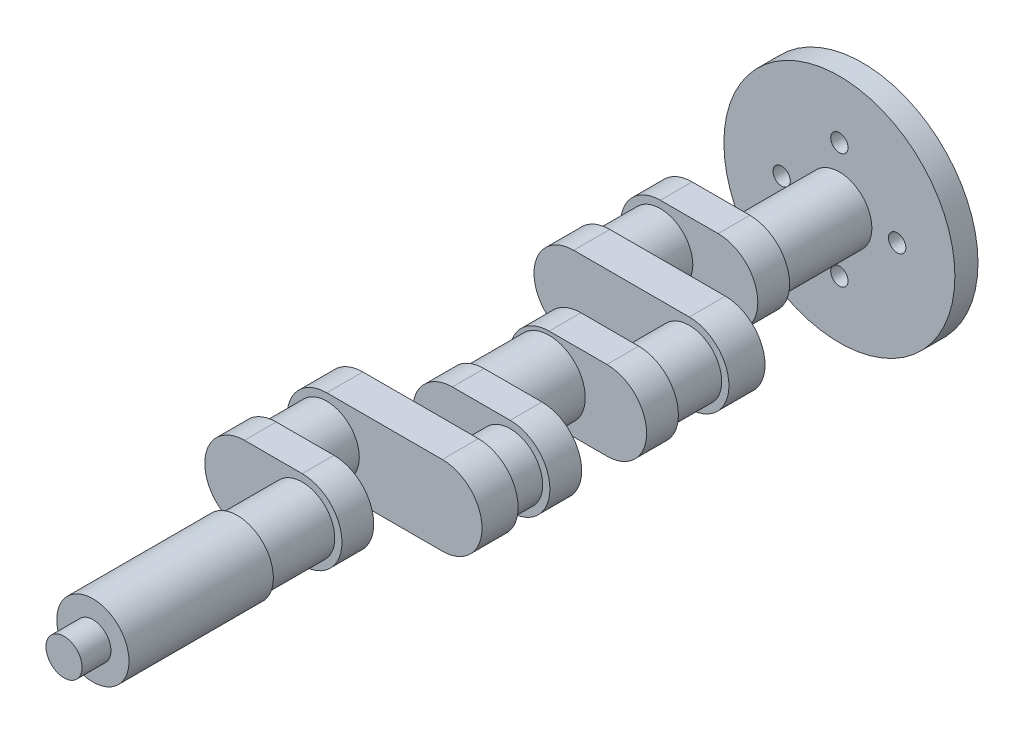
SolidWorks part; units mm, degrees
ref_plane "Front Plane" through (0, 0, 0) normal (0, 0, 1) x (1, 0, 0)
ref_plane "Top Plane" through (0, 0, 0) normal (0, 1, 0) x (1, 0, 0)
ref_plane "Right Plane" through (0, 0, 0) normal (1, 0, 0) x (0, 0, -1)
sketch "Sketch1" plane through (0, 0, 0) normal (0, 0, 1) x (1, 0, 0)
  circle A0 centre (0, 0) radius 80
  dimension "D1" = 160
extrude "Boss-Extrude1" add sketch "Sketch1" along normal blind 16
sketch "Sketch2" plane through (0, 0, 16) normal (0, 0, 1) x (1, 0, 0)
  circle A0 centre (0, 0) radius 22.5
  dimension "D1" = 45
extrude "Boss-Extrude2" add sketch "Sketch2" along normal blind 62
sketch "Sketch3" plane through (0, 0, 78) normal (0, 0, 1) x (1, 0, 0)
  line L0 (0, 0) -> (-40, 0) construction
  line L1 (0, -27.5) -> (-40, -27.5)
  line L2 (0, 27.5) -> (-40, 27.5)
  arc A0 (0, -27.5) -> (0, 27.5) centre (0, 0) ccw
  arc A1 (-40, 27.5) -> (-40, -27.5) centre (-40, 0) ccw
  point P3 (-20, 0)
  dimension "D1" = 27.5
  dimension "D2" = 40
extrude "Boss-Extrude3" add sketch "Sketch3" along normal blind 22
sketch "Sketch4" plane through (0, 0, 100) normal (0, 0, 1) x (1, 0, 0)
  circle A0 centre (-40, 0) radius 22.5
  dimension "D1" = 45
extrude "Boss-Extrude4" add sketch "Sketch4" along normal blind 35
sketch "Sketch5" plane through (0, 0, 135) normal (0, 0, 1) x (1, 0, 0)
  line L0 (-40, 0) -> (40, 0) construction
  line L1 (-40, 27.5) -> (40, 27.5)
  line L2 (-40, -27.5) -> (40, -27.5)
  arc A0 (-40, 27.5) -> (-40, -27.5) centre (-40, 0) ccw
  arc A1 (40, -27.5) -> (40, 27.5) centre (40, 0) ccw
  arc A3 (-40, 27.5) -> (-40, -27.5) centre (-40, 0) ccw construction
  point P4 (0, 0)
  point P9 (0, 0)
  dimension "D1" = 80
extrude "Boss-Extrude5" add sketch "Sketch5" along normal blind 25
sketch "Sketch6" plane through (0, 0, 160) normal (0, 0, 1) x (1, 0, 0)
  circle A0 centre (40, 0) radius 22.5
  dimension "D1" = 45
extrude "Boss-Extrude6" add sketch "Sketch6" along normal blind 35
sketch "Sketch7" plane through (0, 0, 195) normal (0, 0, 1) x (1, 0, 0)
  line L0 (40, 0) -> (0, 0) construction
  line L1 (40, -27.5) -> (0, -27.5)
  line L2 (40, 27.5) -> (0, 27.5)
  arc A0 (40, -27.5) -> (40, 27.5) centre (40, 0) ccw
  arc A1 (0, 27.5) -> (0, -27.5) centre (0, 0) ccw
  arc A2 (40, -27.5) -> (40, 27.5) centre (40, 0) ccw construction
  point P4 (20, 0)
  dimension "D1" = 40
extrude "Boss-Extrude7" add sketch "Sketch7" along normal blind 22
sketch "Sketch8" plane through (0, 0, 217) normal (0, 0, 1) x (1, 0, 0)
  circle A0 centre (0, 0) radius 25
  dimension "D1" = 50
extrude "Boss-Extrude8" add sketch "Sketch8" along normal blind 45
sketch "Sketch9" plane through (0, 0, 262) normal (0, 0, 1) x (1, 0, 0)
  line L2 (40, 27.5) -> (0, 27.5)
  line L3 (0, -27.5) -> (40, -27.5)
  line L4 (40, 27.5) -> (0, 27.5)
  line L5 (0, -27.5) -> (40, -27.5)
  arc A2 (40, -27.5) -> (40, 27.5) centre (40, 0) ccw
  arc A3 (0, 27.5) -> (0, -27.5) centre (0, 0) ccw
  arc A4 (40, -27.5) -> (40, 27.5) centre (40, 0) ccw
  arc A5 (0, 27.5) -> (0, -27.5) centre (0, 0) ccw
  dimension "D1" = 0
extrude "Boss-Extrude9" add sketch "Sketch9" along normal blind 22
sketch "Sketch10" plane through (0, 0, 284) normal (0, 0, 1) x (1, 0, 0)
  circle A0 centre (40, 0) radius 22.5
  dimension "D2" = 45
  dimension "D1" = 40
extrude "Boss-Extrude10" add sketch "Sketch10" along normal blind 22 contours A0
sketch "Sketch11" plane through (0, 0, 306) normal (0, 0, 1) x (1, 0, 0)
  line L0 (40, 0) -> (-40, 0) construction
  line L1 (40, -27.5) -> (-40, -27.5)
  line L2 (40, 27.5) -> (-40, 27.5)
  arc A0 (40, -27.5) -> (40, 27.5) centre (40, 0) ccw
  arc A1 (-40, 27.5) -> (-40, -27.5) centre (-40, 0) ccw
  arc A2 (-40, 27.5) -> (-40, -27.5) centre (-40, 0) ccw construction
  point P3 (0, 0)
extrude "Boss-Extrude11" add sketch "Sketch11" along normal blind 25
sketch "Sketch12" plane through (0, 0, 331) normal (0, 0, 1) x (1, 0, 0)
  circle A0 centre (-40, 0) radius 22.5
  dimension "D1" = 45
extrude "Boss-Extrude12" add sketch "Sketch12" along normal blind 35
sketch "Sketch13" plane through (0, 0, 366) normal (0, 0, 1) x (1, 0, 0)
  line L0 (-40, 0) -> (0, 0) construction
  line L1 (-40, 27.5) -> (0, 27.5)
  line L2 (-40, -27.5) -> (0, -27.5)
  arc A0 (-40, 27.5) -> (-40, -27.5) centre (-40, 0) ccw
  arc A1 (0, -27.5) -> (0, 27.5) centre (0, 0) ccw
  arc A2 (-40, 27.5) -> (-40, -27.5) centre (-40, 0) ccw construction
  point P4 (-20, 0)
  dimension "D1" = 40
extrude "Boss-Extrude13" add sketch "Sketch13" along normal blind 22
sketch "Sketch14" plane through (0, 0, 388) normal (0, 0, 1) x (1, 0, 0)
  circle A0 centre (0, 0) radius 22.5
  dimension "D1" = 45
extrude "Boss-Extrude14" add sketch "Sketch14" along normal blind 45
sketch "Sketch15" plane through (0, 0, 433) normal (0, 0, 1) x (1, 0, 0)
  circle A0 centre (0, 0) radius 25
  dimension "D1" = 50
extrude "Boss-Extrude15" add sketch "Sketch15" along normal blind 100
sketch "Sketch16" plane through (0, 0, 533) normal (0, 0, 1) x (1, 0, 0)
  circle A0 centre (0, 0) radius 12.5
  dimension "D1" = 25
extrude "Boss-Extrude16" add sketch "Sketch16" along normal blind 20
sketch "Sketch17" plane through (0, 0, 0) normal (0, 0, -1) x (-1, 0, 0)
  circle A0 centre (0, 0) radius 40 construction
  circle A2 centre (0, 40) radius 6
  dimension "D1" = 80
  dimension "D2" = 12
extrude "Cut-Extrude1" cut sketch "Sketch17" against normal up to next (16 mm away)
pattern_circular "CirPattern1" count 4 over 360 about axis through (0, 0, 0) along (0, 0, 1) of "Cut-Extrude1"
